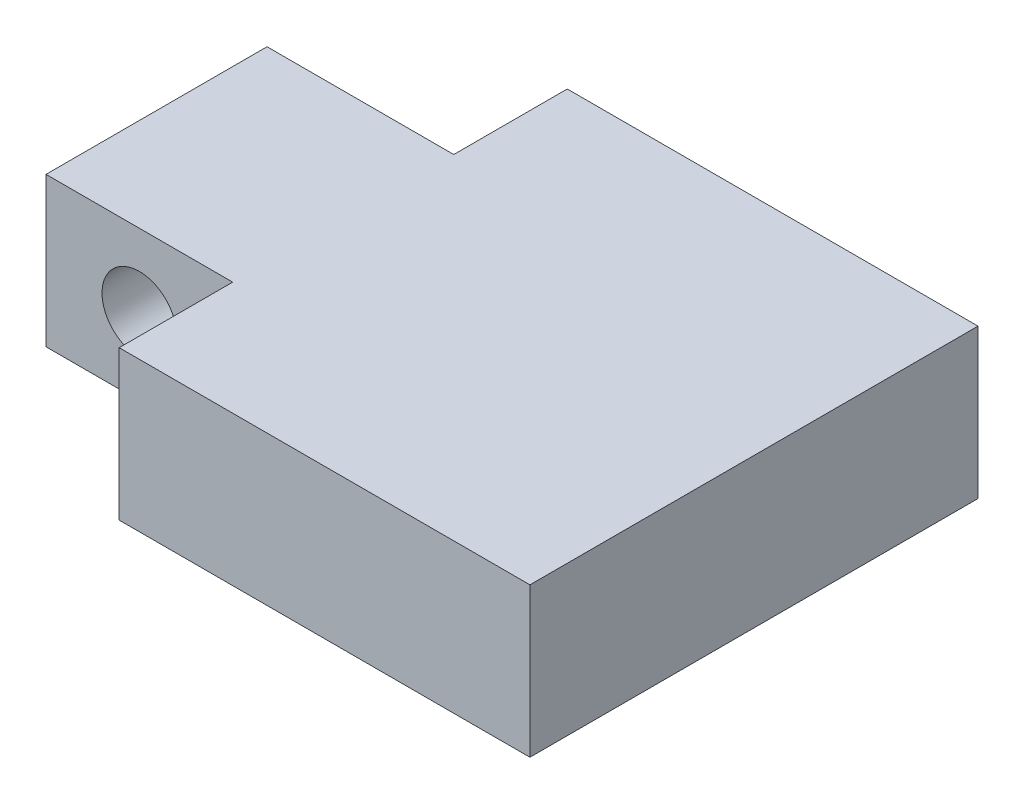
SolidWorks part; units mm, degrees
ref_plane "Front Plane" through (0, 0, 0) normal (0, 0, 1) x (1, 0, 0)
ref_plane "Top Plane" through (0, 0, 0) normal (0, 1, 0) x (1, 0, 0)
ref_plane "Right Plane" through (0, 0, 0) normal (1, 0, 0) x (0, 0, -1)
sketch "Sketch1" plane through (0, 0, 0) normal (0, 1, 0) x (1, 0, 0)
  line L1 (-50.8, -38.1) -> (50.8, -38.1)
  line L2 (-50.8, -38.1) -> (-50.8, 38.1)
  line L3 (-50.8, 38.1) -> (50.8, 38.1)
  line L4 (50.8, -38.1) -> (50.8, 38.1)
  line L5 (-50.8, -38.1) -> (50.8, 38.1) construction
  line L6 (-50.8, 38.1) -> (50.8, -38.1) construction
  point P0 (0, 0)
  dimension "D1" = 101.6
  dimension "D2" = 76.2
extrude "Boss-Extrude1" add sketch "Sketch1" along normal blind 25.4
sketch "Sketch2" plane through (0, 25.4, 0) normal (0, 1, 0) x (1, 0, 0)
  line L0 (-50.8, 0) -> (-50.8, 18.796)
  line L1 (-50.8, 38.1) -> (-50.8, -38.1) construction
  line L2 (-50.8, 18.796) -> (-19.05, 18.796)
  line L3 (-19.05, 18.796) -> (-19.05, 38.1)
  line L4 (50.8, 38.1) -> (-50.8, 38.1) construction
  line L5 (-19.05, 38.1) -> (-50.8, 38.1)
  line L6 (-50.8, 38.1) -> (-50.8, 18.796)
  line L7 (-50.8, 0) -> (-10.5636, 0)
  line L8 (-50.8, -38.1) -> (-50.8, -18.796)
  line L9 (-19.05, -38.1) -> (-50.8, -38.1)
  line L10 (-19.05, -18.796) -> (-19.05, -38.1)
  line L11 (-50.8, -18.796) -> (-19.05, -18.796)
  line M8 (50.8, 38.1) -> (-50.8, 38.1)
  line M9 (-50.8, 38.1) -> (-50.8, -38.1)
  line M10 (-50.8, -38.1) -> (50.8, -38.1)
  dimension "D1" = 18.796
  dimension "D2" = 31.75
extrude "Cut-Extrude2" cut sketch "Sketch2" against normal through all contours L2 L3 M8 M9 | L11 L10 M9 M10
sketch "Sketch4" plane through (0, 0, 18.796) normal (0, 0, 1) x (1, 0, 0)
  line L0 (-50.8, 12.7) -> (-34.925, 12.7)
  line L1 (-50.8, 0) -> (-50.8, 25.4) construction
  circle A0 centre (-34.925, 12.7) radius 6.35
  dimension "D1" = 15.875
extrude "Cut-Extrude3" cut sketch "Sketch4" against normal through all
